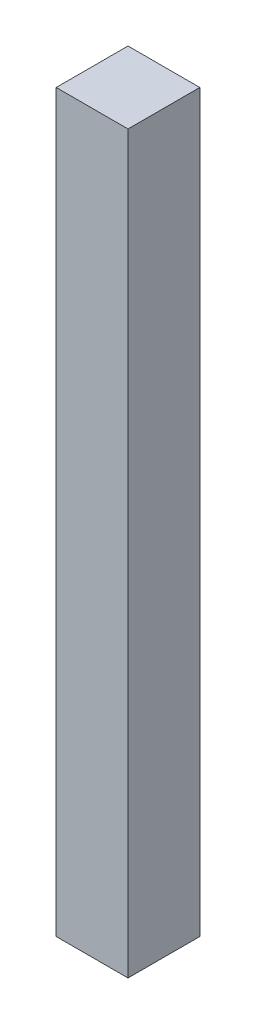
SolidWorks part; units mm, degrees
material "6061 Alloy"
ref_plane "Front Plane" through (0, 0, 0) normal (0, 0, 1) x (1, 0, 0)
ref_plane "Top Plane" through (0, 0, 0) normal (0, 1, 0) x (1, 0, 0)
ref_plane "Right Plane" through (0, 0, 0) normal (1, 0, 0) x (0, 0, -1)
sketch "Sketch1" plane through (0, 0, 0) normal (0, 1, 0) x (1, 0, 0)
  line L1 (-3.15, 3.15) -> (3.15, 3.15)
  line L2 (-3.15, 3.15) -> (-3.15, -3.15)
  line L3 (-3.15, -3.15) -> (3.15, -3.15)
  line L4 (3.15, 3.15) -> (3.15, -3.15)
  line L5 (-3.15, 3.15) -> (3.15, -3.15) construction
  line L6 (-3.15, -3.15) -> (3.15, 3.15) construction
  point P0 (0, 0)
  dimension "D1" = 6.3
extrude "Boss-Extrude1" add sketch "Sketch1" along normal blind 64.5
